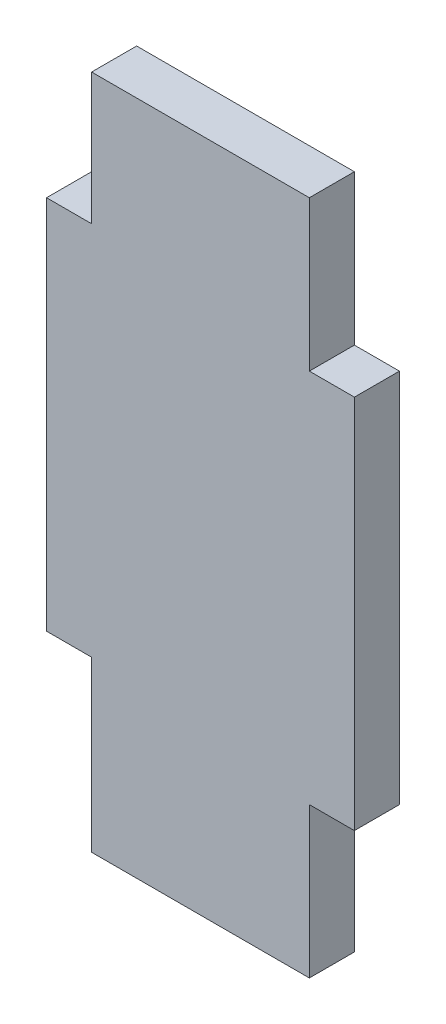
SolidWorks part; units mm, degrees
ref_plane "Plano frontal" through (0, 0, 0) normal (0, 0, 1) x (1, 0, 0)
ref_plane "Plano superior" through (0, 0, 0) normal (0, 1, 0) x (1, 0, 0)
ref_plane "Plano direito" through (0, 0, 0) normal (1, 0, 0) x (0, 0, -1)
sketch "Esboço1" plane through (0, 0, 0) normal (0, 0, 1) x (1, 0, 0)
  line L0 (-47.7707, -6.4583) -> (-47.7707, -17.7083)
  line L1 (-47.7707, 27.2917) -> (-30.2707, 27.2917)
  line L2 (-47.7707, 27.2917) -> (-47.7707, 18.5417)
  line L3 (-47.7707, -17.7083) -> (-30.2707, -17.7083)
  line L4 (-30.2707, 27.2917) -> (-30.2707, -17.7083)
  line L5 (-47.7707, -6.4583) -> (-50.7707, -6.4583)
  line L7 (-47.7707, 18.5417) -> (-50.7707, 18.5417)
  line L8 (-50.7707, -6.4583) -> (-50.7707, 18.5417)
  dimension "D1" = 25
  dimension "D2" = 45
  dimension "D3" = 17.5
  dimension "D4" = 3
extrude "Ressalto-extrusão1" add sketch "Esboço1" along normal blind 3
sketch "Esboço2" plane through (0, 0, 3) normal (0, 0, 1) x (1, 0, 0)
  line L1 (-30.2707, 27.2917) -> (-33.2707, 27.2917)
  line L2 (-30.2707, 27.2917) -> (-30.2707, 17.2917)
  line L3 (-30.2707, 17.2917) -> (-33.2707, 17.2917)
  line L4 (-33.2707, 27.2917) -> (-33.2707, 17.2917)
  line L5 (-30.2707, -17.7083) -> (-33.2707, -17.7083)
  line L6 (-30.2707, -17.7083) -> (-30.2707, -7.7083)
  line L7 (-30.2707, -7.7083) -> (-33.2707, -7.7083)
  line L8 (-33.2707, -17.7083) -> (-33.2707, -7.7083)
  dimension "D1" = 10
  dimension "D2" = 10
  dimension "D3" = 3
  dimension "D4" = 3
extrude "Corte-extrusão1" cut sketch "Esboço2" against normal blind 3
